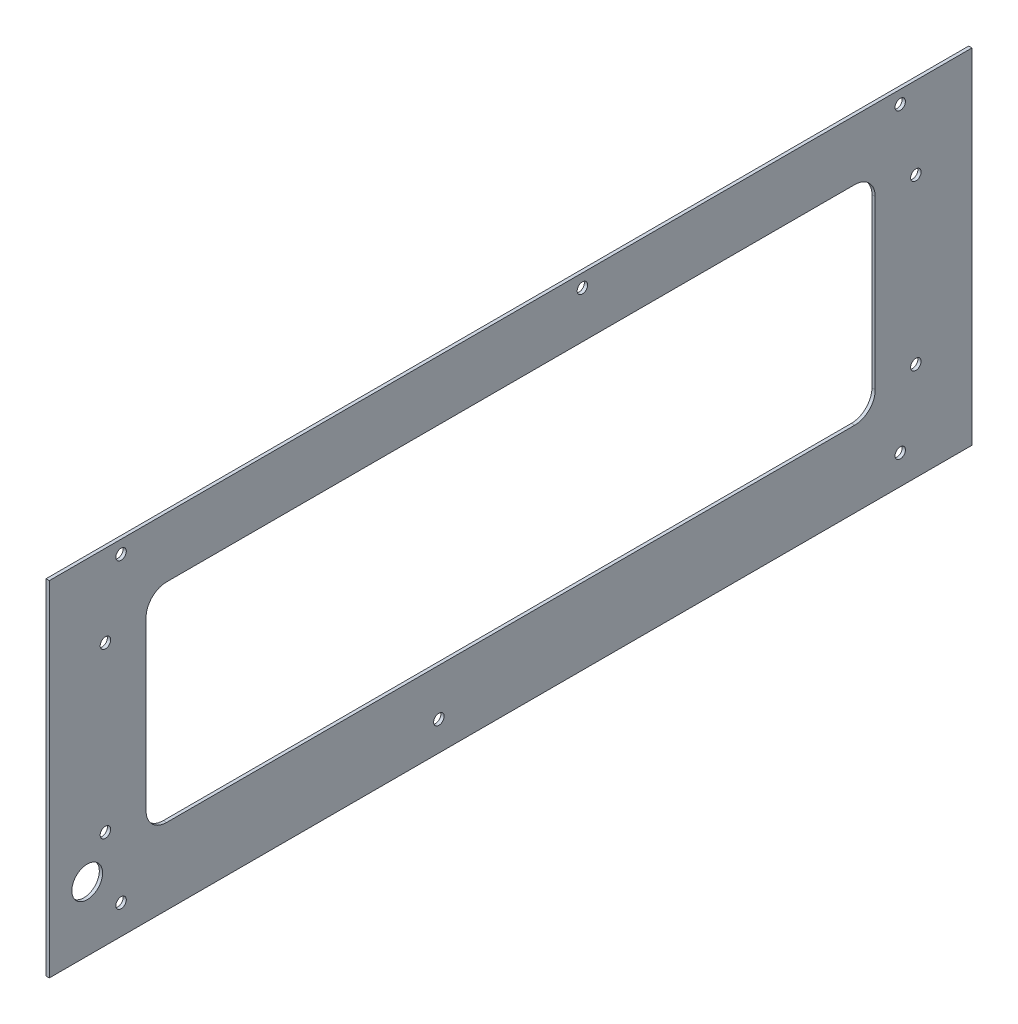
SolidWorks part; units mm, degrees
material "6061-T6 (SS)"
ref_plane "Front Plane" through (0, 0, 0) normal (0, 0, 1) x (1, 0, 0)
ref_plane "Top Plane" through (0, 0, 0) normal (0, 1, 0) x (1, 0, 0)
ref_plane "Right Plane" through (0, 0, 0) normal (1, 0, 0) x (0, 0, -1)
sketch "Sketch1" plane through (0, 0, 0) normal (1, 0, 0) x (0, 0, -1)
  line L0 (0, 0) -> (0, 49.1742) construction
  line L1 (-190, -73.5911) -> (190, -73.5911) construction
  line L2 (-190, -73.5911) -> (-190, 73.5911) construction
  line L3 (-190, 73.5911) -> (190, 73.5911) construction
  line L4 (190, -73.5911) -> (190, 73.5911) construction
  line L5 (-190, -73.5911) -> (190, 73.5911) construction
  line L6 (-190, 73.5911) -> (190, -73.5911) construction
  line L7 (-225, 79.9538) -> (225, 79.9538)
  line L8 (-225, 79.9538) -> (-225, -87.8786)
  line L9 (-225, -87.8786) -> (225, -87.8786)
  line L10 (225, 79.9538) -> (225, -87.8786)
  line L11 (-35, 73.5911) -> (-35, -73.5911) construction
  line L12 (35, 73.5911) -> (35, -73.5911) construction
  point P0 (0, 0)
  point P12 (0, 79.9538)
  dimension "D1" = 380
  dimension "D2" = 147.1822
  dimension "D3" = 6.3627
  dimension "D4" = 14.2875
  dimension "D5" = 450
  dimension "D6" = 35
extrude "Boss-Extrude1" add sketch "Sketch1" along normal blind 1.6002
hole_wizard "#10 Clearance Hole1" positions "Sketch3" profile "Sketch2" hole size "#10" standard "ANSI Inch"
sketch "Sketch3" plane through (1.6002, 0, 0) normal (1, 0, 0) x (0, 0, -1)
  point P0 (-190, 73.5911)
  point P3 (35, 73.5911)
  point P6 (-35, -73.5911)
  point P9 (-190, -73.5911)
  point P12 (190, 73.5911)
  point P15 (190, -73.5911)
sketch "Sketch2" plane through (1.6002, 73.5911, 190) normal (0, 1, 0) x (0, 0, -1)
  line L0 (0, 0) -> (0, 131.0638)
  line L1 (0, 131.0638) -> (2.5527, 129.53)
  line L2 (2.5527, 129.53) -> (2.5527, 0)
  line L5 (2.5527, 0) -> (0, 0)
  line L10 (0, 131.0638) -> (-2.5527, 129.53) construction
  line L11 (0, -6.35) -> (0, 107.95) construction
  dimension "Hole Dia." = 5.1054
  dimension "Hole Depth" = 129.53
  dimension "Drill Angle" = 118
sketch "Sketch4" plane through (1.6002, 0, 0) normal (1, 0, 0) x (0, 0, -1)
  line L0 (-225, -87.8786) -> (225, -87.8786) construction
  line L1 (-225, 79.9538) -> (-225, -87.8786) construction
  circle A0 centre (-206.5, -56.5321) radius 7.5
  dimension "D1" = 15
  dimension "D2" = 31.3465
  dimension "D3" = 18.5
extrude "Cut-Extrude1" cut sketch "Sketch4" against normal through all
sketch "Sketch5" plane through (1.6002, 0, 0) normal (1, 0, 0) x (0, 0, -1)
  line L0 (-177.8, 50.8) -> (177.8, -50.8) construction
  line L1 (-177.8, 50.8) -> (177.8, 50.8)
  line L2 (-177.8, 50.8) -> (-177.8, -50.8)
  line L3 (-177.8, -50.8) -> (177.8, -50.8)
  line L4 (177.8, 50.8) -> (177.8, -50.8)
  point P4 (0, 0)
  dimension "D1" = 355.6
  dimension "D2" = 101.6
extrude "Cut-Extrude2" cut sketch "Sketch5" against normal through all
fillet "Fillet1" radius 10 4 edges at (0.8001, -50.8, 177.8) (0.8001, -50.8, -177.8) (0.8001, 50.8, -177.8) (0.8001, 50.8, 177.8)
hole_wizard "#10 Clearance Hole2" positions "Sketch7" profile "Sketch6" hole size "#10" standard "ANSI Inch" end condition through all
sketch "Sketch7" plane through (1.6002, 0, 0) normal (1, 0, 0) x (0, 0, -1)
  line L0 (0, 0) -> (39.8933, 0) construction
  line L1 (0, 0) -> (0, 34.5624) construction
  point P0 (197.627, 40)
  dimension "D1" = 197.627
  dimension "D2" = 40
sketch "Sketch6" plane through (1.6002, 40, -197.627) normal (0, 1, 0) x (0, 0, -1)
  line L0 (0, 0) -> (0, 1.6002)
  line L1 (0, 1.6002) -> (2.5527, 1.6002)
  line L2 (2.5527, 1.6002) -> (2.5527, 0)
  line L5 (2.5527, 0) -> (0, 0)
  line L11 (0, -6.35) -> (0, 107.95) construction
  dimension "Thru Hole Dia." = 5.1054
  dimension "Thru Hole Depth" = 1.6002
mirror "Mirror1" about plane through (0, 0, 0) normal (0, 1, 0) of "#10 Clearance Hole2"
mirror "Mirror2" about plane through (0, 0, 0) normal (0, 0, 1) of "Mirror1", "#10 Clearance Hole2"
